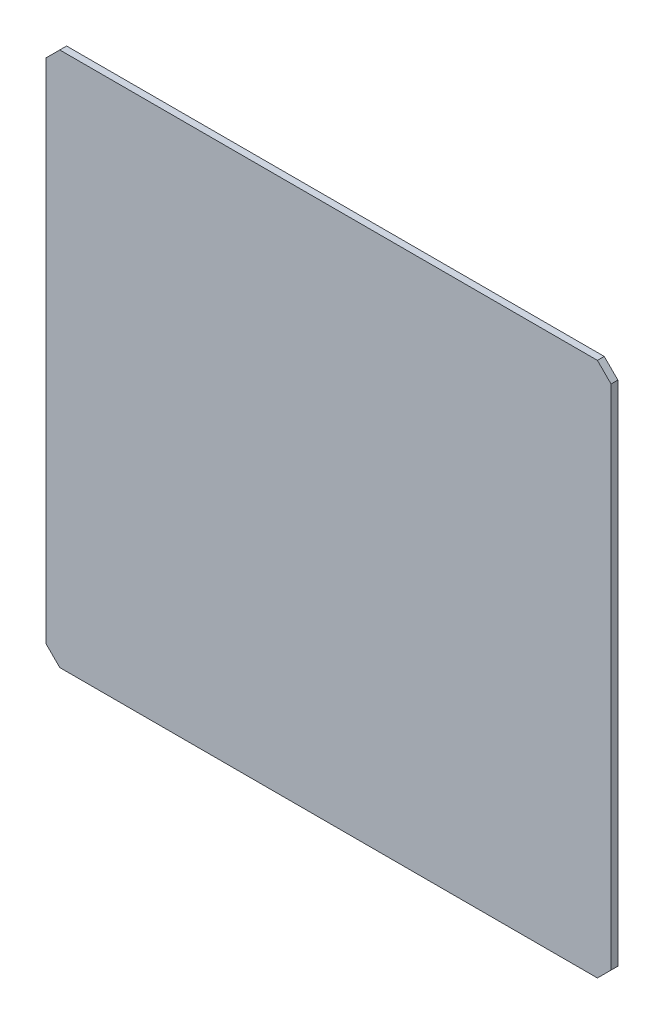
SolidWorks part; units mm, degrees
material "Acrilico (impatto medio-alto)"
ref_plane "Piano frontale" through (0, 0, 0) normal (0, 0, 1) x (1, 0, 0)
ref_plane "Piano superiore" through (0, 0, 0) normal (0, 1, 0) x (1, 0, 0)
ref_plane "Piano destro" through (0, 0, 0) normal (1, 0, 0) x (0, 0, -1)
sketch "Schizzo1" plane through (0, 0, 0) normal (0, 0, 1) x (1, 0, 0)
  line L0 (-207, 186) -> (-197, 196)
  line L1 (197, -196) -> (-197, -196)
  line L2 (207, -186) -> (207, 186)
  line L3 (197, 196) -> (-197, 196)
  line L4 (-207, -186) -> (-207, 186)
  line L5 (207, -196) -> (-207, 196) construction
  line L6 (207, 196) -> (-207, -196) construction
  line L7 (207, 186) -> (197, 196)
  line L8 (197, -196) -> (207, -186)
  line L9 (-197, -196) -> (-207, -186)
  point P0 (0, 0)
  dimension "D1" = 414
  dimension "D2" = 392
extrude "Estrusione-Estrusione1" add sketch "Schizzo1" along normal blind 5 contours L4 L0 L3 L7 L2 L8 L1 L9
